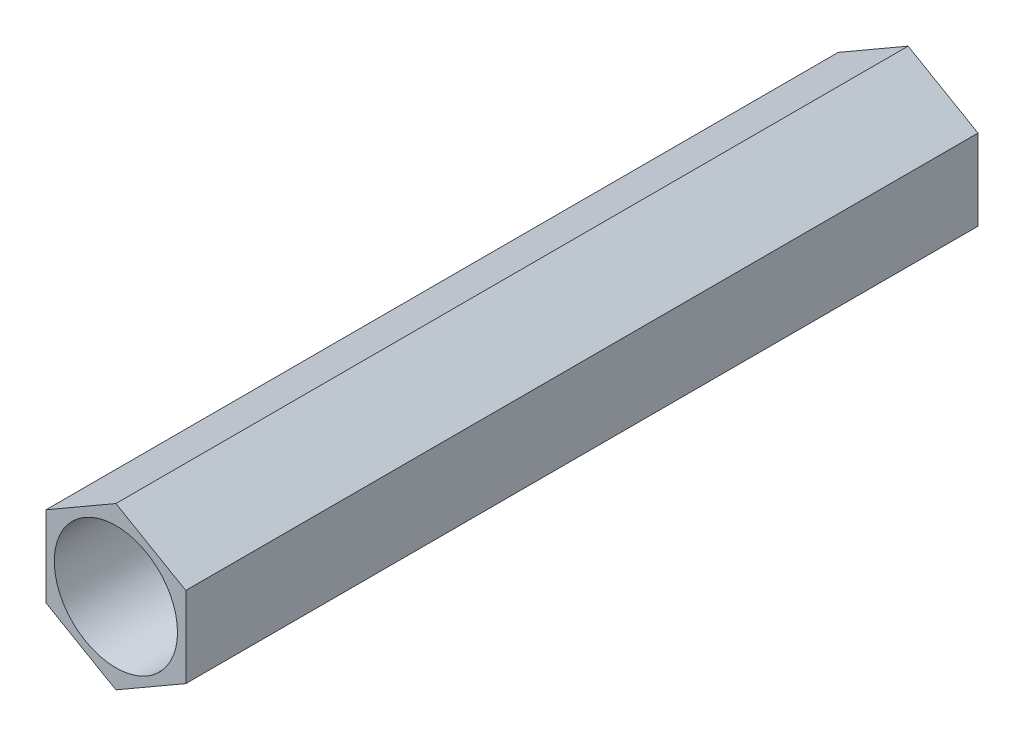
SolidWorks part; units mm, degrees
ref_plane "Front Plane" through (0, 0, 0) normal (0, 0, 1) x (1, 0, 0)
ref_plane "Top Plane" through (0, 0, 0) normal (0, 1, 0) x (1, 0, 0)
ref_plane "Right Plane" through (0, 0, 0) normal (1, 0, 0) x (0, 0, -1)
sketch "Sketch1" plane through (0, 0, 0) normal (0, 0, 1) x (1, 0, 0)
  line L1 (0, -2.75) -> (2.3816, -1.375)
  line L2 (2.3816, -1.375) -> (2.3816, 1.375)
  line L3 (2.3816, 1.375) -> (0, 2.75)
  line L4 (0, 2.75) -> (-2.3816, 1.375)
  line L5 (-2.3816, 1.375) -> (-2.3816, -1.375)
  line L6 (-2.3816, -1.375) -> (0, -2.75)
  circle A0 centre (0, 0) radius 2.3816 construction
  circle A1 centre (0, 0) radius 2.1
  dimension "D2" = 4.2
  dimension "D1" = 2.75
extrude "Extrude1" add sketch "Sketch1" along normal blind 27
